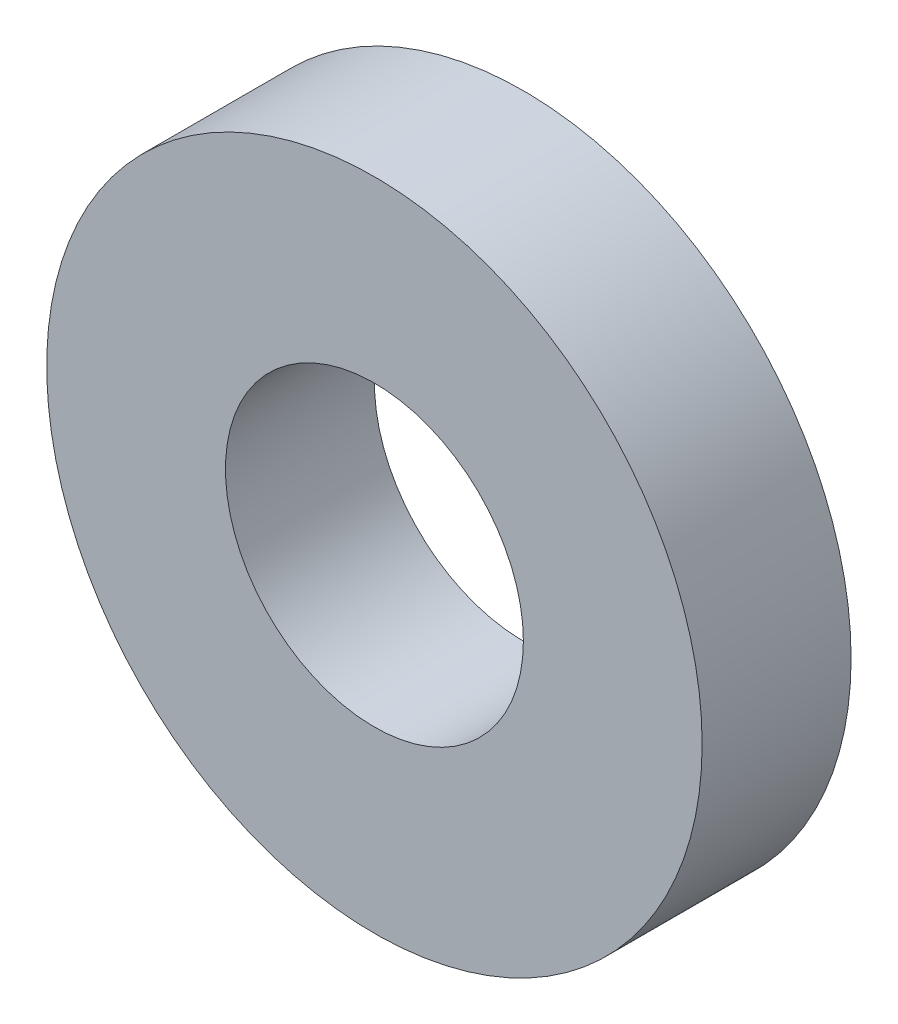
SolidWorks part; units mm, degrees
ref_plane "Front Plane" through (0, 0, 0) normal (0, 0, 1) x (1, 0, 0)
ref_plane "Top Plane" through (0, 0, 0) normal (0, 1, 0) x (1, 0, 0)
ref_plane "Right Plane" through (0, 0, 0) normal (1, 0, 0) x (0, 0, -1)
sketch "Sketch1" plane through (0, 0, 0) normal (0, 0, 1) x (1, 0, 0)
  circle A0 centre (0, 0) radius 6
  circle A1 centre (0, 0) radius 13.2
extrude "Boss-Extrude1" add sketch "Sketch1" along normal blind 6
sketch "Sketch2" plane through (0, 0, 6) normal (0, 0, 1) x (1, 0, 0)
  line L0 (0, 0) -> (0, 15.2) construction
  line L1 (-1.8199, 15.2) -> (0, 0) construction
  line L2 (1.8199, 15.2) -> (0, 0) construction
  line L3 (-1122.4778, 12) -> (1122.4778, 12)
  arc A0 (-2.8199, 12.8953) -> (2.8199, 12.8953) centre (0, 0) cw
  arc A1 (-1.8199, 10.32) -> (1.8199, 10.32) centre (0, 0) cw
  arc A2 (-2.8199, 12.8953) -> (-1.8199, 10.32) centre (-562.4742, -205.9038) ccw
  arc A3 (2.8199, 12.8953) -> (1.8199, 10.32) centre (562.4742, -205.9038) cw
